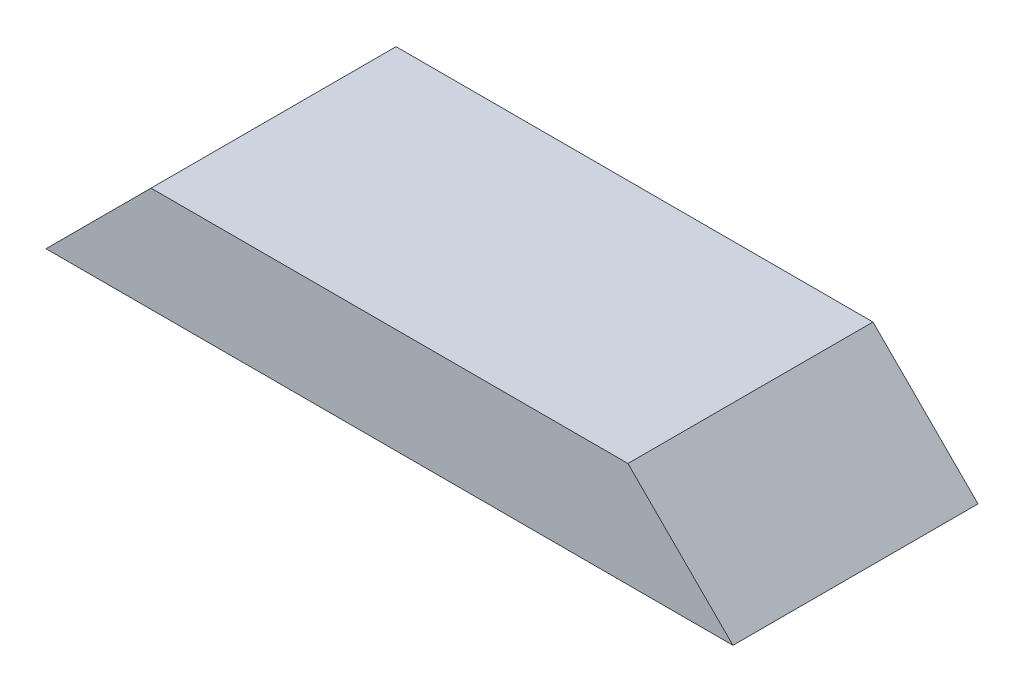
SolidWorks part; units mm, degrees
ref_plane "Front Plane" through (0, 0, 0) normal (0, 0, 1) x (1, 0, 0)
ref_plane "Top Plane" through (0, 0, 0) normal (0, 1, 0) x (1, 0, 0)
ref_plane "Right Plane" through (0, 0, 0) normal (1, 0, 0) x (0, 0, -1)
sketch "Sketch1" plane through (0, 0, 0) normal (0, 1, 0) x (1, 0, 0)
  line L1 (0, 0) -> (249.2375, 0)
  line L2 (0, 0) -> (0, 88.9)
  line L3 (0, 88.9) -> (249.2375, 88.9)
  line L4 (249.2375, 0) -> (249.2375, 88.9)
  dimension "D1" = 88.9
  dimension "D2" = 249.2375
extrude "Boss-Extrude1" add sketch "Sketch1" along normal blind 38.1
sketch "Sketch2" plane through (0, 0, 0) normal (0, 0, 1) x (1, 0, 0)
  line L0 (0, 0) -> (38.1, 38.1)
  line L1 (0, 38.1) -> (249.2375, 38.1) construction
  line L2 (0, 38.1) -> (0, 0)
  line L3 (249.2375, 0) -> (211.1375, 38.1)
  line L4 (211.1375, 38.1) -> (249.2375, 38.1)
  line L5 (249.2375, 38.1) -> (249.2375, 0)
  line L6 (38.1, 38.1) -> (0, 38.1)
  dimension "D1" = 38.1
  dimension "D2" = 38.1
extrude "Cut-Extrude1" cut sketch "Sketch2" against normal through all
